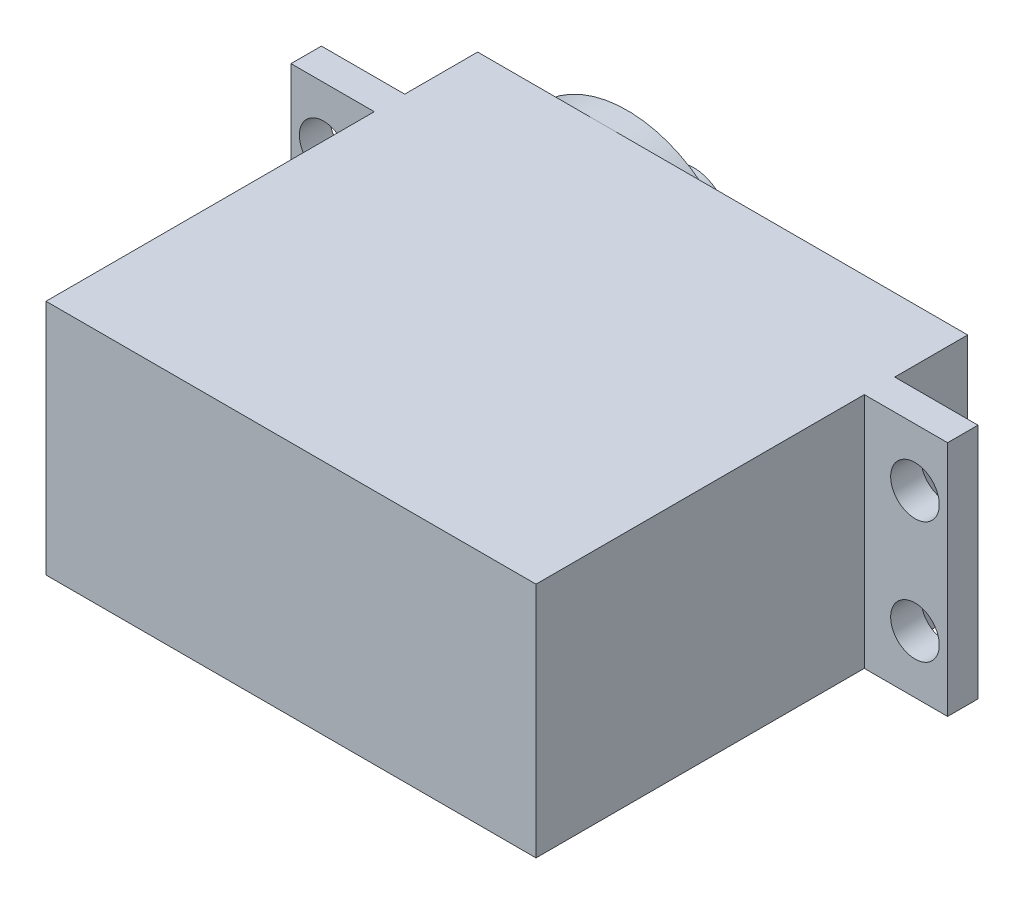
SolidWorks part; units mm, degrees
ref_plane "前视基准面" through (0, 0, 0) normal (0, 0, 1) x (1, 0, 0)
ref_plane "上视基准面" through (0, 0, 0) normal (0, 1, 0) x (1, 0, 0)
ref_plane "右视基准面" through (0, 0, 0) normal (1, 0, 0) x (0, 0, -1)
sketch "草图1" plane through (0, 0, 0) normal (0, 0, 1) x (1, 0, 0)
  line L1 (20.15, -9.75) -> (-20.15, -9.75)
  line L2 (20.15, -9.75) -> (20.15, 9.75)
  line L3 (20.15, 9.75) -> (-20.15, 9.75)
  line L4 (-20.15, -9.75) -> (-20.15, 9.75)
  line L5 (20.15, -9.75) -> (-20.15, 9.75) construction
  line L6 (20.15, 9.75) -> (-20.15, -9.75) construction
  point P0 (0, 0)
  dimension "D1" = 19.5
  dimension "D2" = 40.3
extrude "凸台-拉伸1" add sketch "草图1" along normal blind 27
sketch "草图2" plane through (0, 0, 0) normal (0, 0, -1) x (-1, 0, 0)
  line L0 (20.15, 9.75) -> (20.15, -9.75)
  line L1 (27, -9.75) -> (-27, -9.75)
  line L2 (27, -9.75) -> (27, 9.75)
  line L3 (27, 9.75) -> (-27, 9.75)
  line L4 (-27, -9.75) -> (-27, 9.75)
  line L5 (27, -9.75) -> (-27, 9.75) construction
  line L6 (27, 9.75) -> (-27, -9.75) construction
  line L7 (-20.15, 9.75) -> (-20.15, -9.75)
  line L8 (20.15, 9.75) -> (20.15, -9.75) construction
  line L9 (0, 42.1169) -> (0, -13.7788)
  circle A0 centre (24.315, 5) radius 2
  circle A1 centre (24.315, -5) radius 2
  circle A2 centre (-24.315, -5) radius 2
  circle A3 centre (-24.315, 5) radius 2
  point P0 (0, 0)
  point P22 (0, 14.169)
  line M9 (20.15, -9.75) -> (20.15, 9.75)
  line M10 (20.15, 9.75) -> (-20.15, 9.75)
  line M11 (-20.15, 9.75) -> (-20.15, -9.75)
  line M12 (-20.15, -9.75) -> (20.15, -9.75)
  dimension "D7" = 4
  dimension "D8" = 4
  dimension "D1" = 19.5
  dimension "D2" = 54
  dimension "D3" = 48.63
  dimension "D4" = 48.63
  dimension "D5" = 10
extrude "凸台-拉伸2" add sketch "草图2" along normal blind 2.5 contours L2 L3 L1 A1 A0 M9 | L9 L1 M10 M9 | L4 L1 L3 A2 A3 M11 | L9 L3 M11 M12
sketch "草图3" plane through (0, 0, -2.5) normal (0, 0, -1) x (-1, 0, 0)
  line L6 (20.15, 9.75) -> (-20.15, 9.75)
  line L7 (20.15, 9.75) -> (20.15, -9.75)
  line L8 (20.15, -9.75) -> (-20.15, -9.75)
  line L9 (-20.15, 9.75) -> (-20.15, -9.75)
  line L10 (20.15, 9.75) -> (-20.15, -9.75) construction
  line L11 (20.15, -9.75) -> (-20.15, 9.75) construction
  point P0 (0, 0)
  point P1 (0, 0)
  dimension "D1" = 40.3
  dimension "D2" = 19.5
extrude "凸台-拉伸3" add sketch "草图3" along normal blind 6
sketch "草图4" plane through (0, 0, -8.5) normal (0, 0, -1) x (-1, 0, 0)
  line L0 (27, -9.75) -> (27, 9.75) construction
  line L1 (20.15, 9.75) -> (-20.15, 9.75) construction
  line L2 (9.85, 9.75) -> (-15.2111, 9.75)
  line L3 (-7.6091, 0) -> (35.1807, 0) construction
  line L5 (3.7741, 7.6253) -> (-15.2111, 7.6253)
  line L6 (-15.2111, 7.6253) -> (-15.2111, -7.6253)
  line L7 (-15.2111, -7.6253) -> (3.7741, -7.6253)
  arc A0 (3.7741, -7.6253) -> (3.7741, 7.6253) centre (9.85, 0) ccw
  point P8 (3.7741, 7.6253)
  point P14 (3.7741, -7.6253)
  dimension "D2" = 19.5
  dimension "D4" = 18.9851
  dimension "D1" = 17.15
  dimension "D3" = 9.75
  dimension "D5" = 18.9851
  dimension "D6" = 15.2506
extrude "凸台-拉伸4" add sketch "草图4" along normal blind 2
sketch "草图5" plane through (0, 0, -10.5) normal (0, 0, -1) x (-1, 0, 0)
  line L0 (20.15, 9.75) -> (9.85, 9.75) construction
  line L2 (27, -9.75) -> (27, 9.75) construction
  circle A0 centre (9.85, 0) radius 6
  dimension "D1" = 12
  dimension "D2" = 9.75
  dimension "D3" = 17.15
extrude "凸台-拉伸5" add sketch "草图5" along normal blind 1 contours A0
sketch "草图6" plane through (0, 0, -11.5) normal (0, 0, -1) x (-1, 0, 0)
  line L0 (20.15, 9.75) -> (9.85, 9.75) construction
  line L1 (27, -9.75) -> (27, 9.75) construction
  circle A0 centre (9.85, 0) radius 2.9
  dimension "D3" = 5.8
  dimension "D1" = 9.75
  dimension "D2" = 17.15
extrude "凸台-拉伸6" add sketch "草图6" along normal blind 4.5 contours A0
sketch "草图7" plane through (0, 0, -16) normal (0, 0, -1) x (-1, 0, 0)
  circle A0 centre (9.85, 0) radius 1.5
  dimension "D1" = 3
extrude "切除-拉伸1" cut sketch "草图7" against normal up to surface (4.5 mm away) contours A0 up to face at (-12.75, 0, -11.5)
